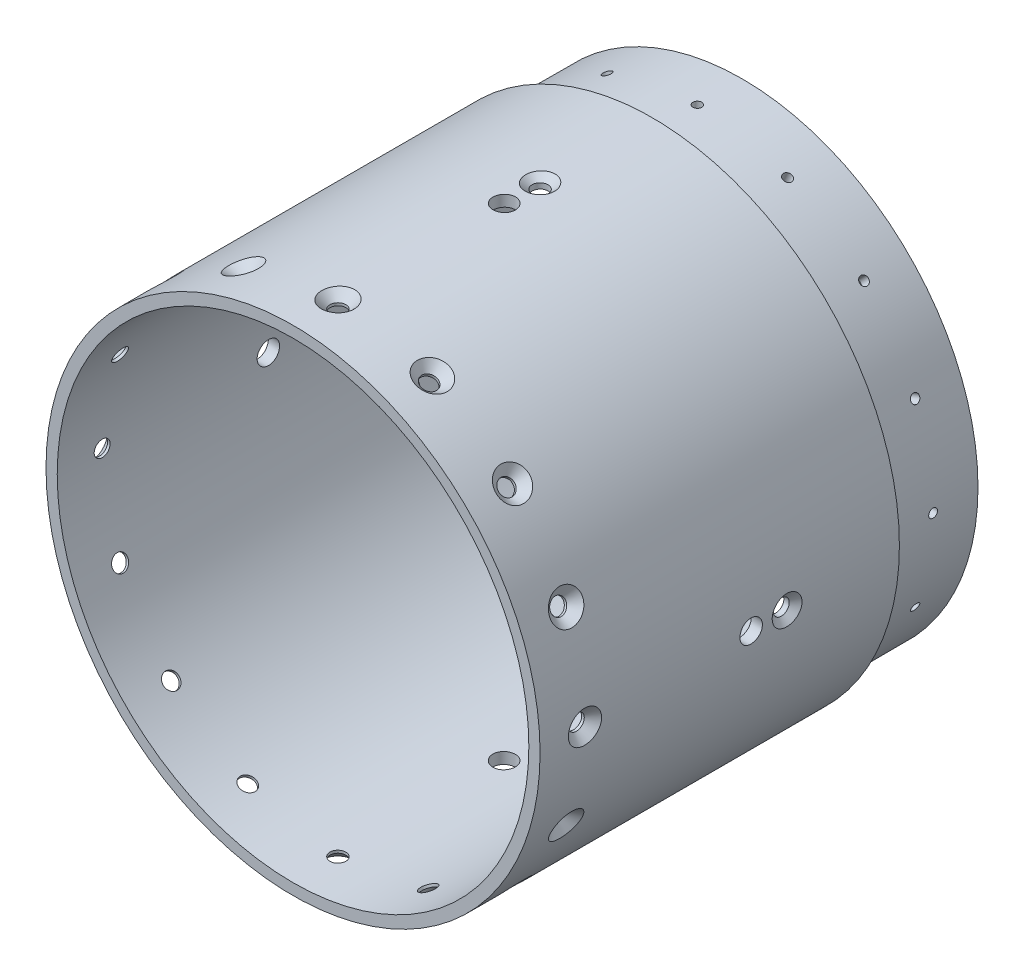
SolidWorks part; units mm, degrees
ref_plane "Front Plane" through (0, 0, 0) normal (0, 0, 1) x (1, 0, 0)
ref_plane "Top Plane" through (0, 0, 0) normal (0, 1, 0) x (1, 0, 0)
ref_plane "Right Plane" through (0, 0, 0) normal (1, 0, 0) x (0, 0, -1)
sketch "Sketch1" plane through (0, 0, 0) normal (0, 0, 1) x (1, 0, 0)
  circle A0 centre (0, 0) radius 63.5
  circle A1 centre (0, 0) radius 69.85
extrude "Extrude1" add sketch "Sketch1" along normal blind 127
sketch "Sketch4" plane through (0, 0, 0) normal (0, 0, -1) x (-1, 0, 0)
  circle A0 centre (0, 0) radius 66.675
extrude "Extrude2" cut sketch "Sketch4" against normal blind 25.4 flip side to cut
sketch "Sketch5" plane through (0, 0, 127) normal (0, 0, 1) x (1, 0, 0)
  circle A0 centre (0, 0) radius 66.675
extrude "Extrude3" cut sketch "Sketch5" against normal blind 95.25
ref_plane "Plane1" through (0, 0, 12.7) normal (0, 0, 1) x (1, 0, 0)
sketch "Sketch6" plane through (0, 0, 12.7) normal (0, 0, 1) x (1, 0, 0)
  line L0 (0, 0) -> (-66.675, 0) construction
  circle A0 centre (0, 0) radius 66.675 construction
ref_plane "Plane2" through (-66.675, 0, 12.7) normal (-1, 0, 0) x (0, 0, 1)
hole_wizard "#40 (0.098) Diameter Hole2" positions "Sketch10" profile "Sketch9" hole size "#40" standard "Ansi Inch"
sketch "Sketch10" plane through (-66.675, 0, 12.7) normal (-1, 0, 0) x (0, 0, 1)
  point P1 (0, 0)
sketch "Sketch9" plane through (-66.675, 0, 12.7) normal (0, 1, 0) x (0, 0, 1)
  line L0 (0, 0) -> (0, 13.4478)
  line L1 (0, 13.4478) -> (1.2446, 12.7)
  line L2 (1.2446, 12.7) -> (1.2446, 0)
  line L5 (1.2446, 0) -> (0, 0)
  line L10 (0, 13.4478) -> (-1.2446, 12.7) construction
  line L11 (0, -6.35) -> (0, 107.95) construction
  dimension "Hole Dia." = 2.4892
  dimension "Hole Depth" = 12.7
  dimension "Drill Angle" = 118
ref_plane "Plane3" through (0, 0, 114.3) normal (0, 0, 1) x (1, 0, 0)
sketch "Sketch11" plane through (0, 0, 114.3) normal (0, 0, 1) x (1, 0, 0)
  line L0 (0, 0) -> (69.85, 0) construction
  circle A0 centre (0, 0) radius 69.85 construction
ref_plane "Plane4" through (69.85, 0, 114.3) normal (1, 0, 0) x (0, 0, -1)
hole_wizard "CSK for M4 Flat Head Machine Screw1" positions "Sketch13" profile "Sketch12" countersink size "M4" standard "Ansi Metric"
sketch "Sketch13" plane through (69.85, 0, 114.3) normal (1, 0, 0) x (0, 0, -1)
  point P1 (0, 0)
sketch "Sketch12" plane through (69.85, 0, 114.3) normal (0, 1, 0) x (0, 0, -1)
  line L0 (0, 0) -> (0, 13.5439)
  line L1 (0, 13.5439) -> (2.25, 12.192)
  line L2 (2.25, 12.192) -> (2.25, 2.45)
  line L3 (2.25, 2.45) -> (4.7, 0)
  line L5 (4.7, 0) -> (0, 0)
  line L6 (-2.25, 2.45) -> (-4.7, 0) construction
  line L10 (0, 13.5439) -> (-2.25, 12.192) construction
  line L11 (0, -6.35) -> (0, 107.95) construction
  dimension "Hole Dia." = 4.5
  dimension "Hole Depth" = 12.192
  dimension "Near C'Sink Dia." = 9.4
  dimension "Near C'Sink Angle" = 90
  dimension "Drill Angle" = 118
pattern_circular "CirPattern1" count 16 over 360 about axis through (0, 0, 127) along (0, 0, -1) of "#40 (0.098) Diameter Hole2", "CSK for M4 Flat Head Machine Screw1"
ref_plane "Plane5" through (0, 0, 67.31) normal (0, 0, 1) x (1, 0, 0)
sketch "Sketch14" plane through (0, 0, 67.31) normal (0, 0, 1) x (1, 0, 0)
  line L0 (0, 0) -> (0, -69.85) construction
  line L1 (0, -69.7734) -> (0, -67.4) construction
  circle A0 centre (0, 0) radius 69.85 construction
ref_plane "Plane6" through (0, -69.85, 67.31) normal (0, -1, 0) x (1, 0, 0)
sketch "Sketch15" plane through (0, -69.85, 67.31) normal (0, -1, 0) x (1, 0, 0)
  line L0 (0, 0.1207) -> (0, -10.16) construction
hole_wizard "E (0.25) Diameter Hole2" positions "Sketch18" profile "Sketch17" hole size "E" standard "Ansi Inch"
sketch "Sketch18" plane through (0, -69.85, 67.31) normal (0, -1, 0) x (1, 0, 0)
  point P1 (0, 0)
sketch "Sketch17" plane through (0, -69.85, 67.31) normal (1, 0, 0) x (0, 0, -1)
  line L0 (0, 0) -> (0, 14.6077)
  line L1 (0, 14.6077) -> (3.175, 12.7)
  line L2 (3.175, 12.7) -> (3.175, 0)
  line L5 (3.175, 0) -> (0, 0)
  line L10 (0, 14.6077) -> (-3.175, 12.7) construction
  line L11 (0, -6.35) -> (0, 107.95) construction
  dimension "Hole Dia." = 6.35
  dimension "Hole Depth" = 12.7
  dimension "Drill Angle" = 118
hole_wizard "CSK for #8 Flat Head Machine Screw (100)2" positions "Sketch21" profile "Sketch22" countersink size "#8" standard "Ansi Inch"
sketch "Sketch21" plane through (0, -69.85, 67.31) normal (0, -1, 0) x (1, 0, 0)
  point P1 (0, -10.16)
sketch "Sketch22" plane through (0, -69.85, 57.15) normal (1, 0, 0) x (0, 0, -1)
  line L0 (0, 0) -> (0, 13.5427)
  line L1 (0, 13.5427) -> (2.2479, 12.192)
  line L2 (2.2479, 12.192) -> (2.2479, 1.6518)
  line L3 (2.2479, 1.6518) -> (4.2164, 0)
  line L5 (4.2164, 0) -> (0, 0)
  line L6 (-2.2479, 1.6518) -> (-4.2164, 0) construction
  line L10 (0, 13.5427) -> (-2.2479, 12.192) construction
  line L11 (0, -6.35) -> (0, 107.95) construction
  dimension "Hole Dia." = 4.4958
  dimension "Hole Depth" = 12.192
  dimension "Near C'Sink Dia." = 8.4328
  dimension "Near C'Sink Angle" = 100
  dimension "Drill Angle" = 118
pattern_circular "CirPattern2" count 4 over 360 about axis through (0, 0, 127) along (0, 0, -1) of "E (0.25) Diameter Hole2", "CSK for #8 Flat Head Machine Screw (100)2"
